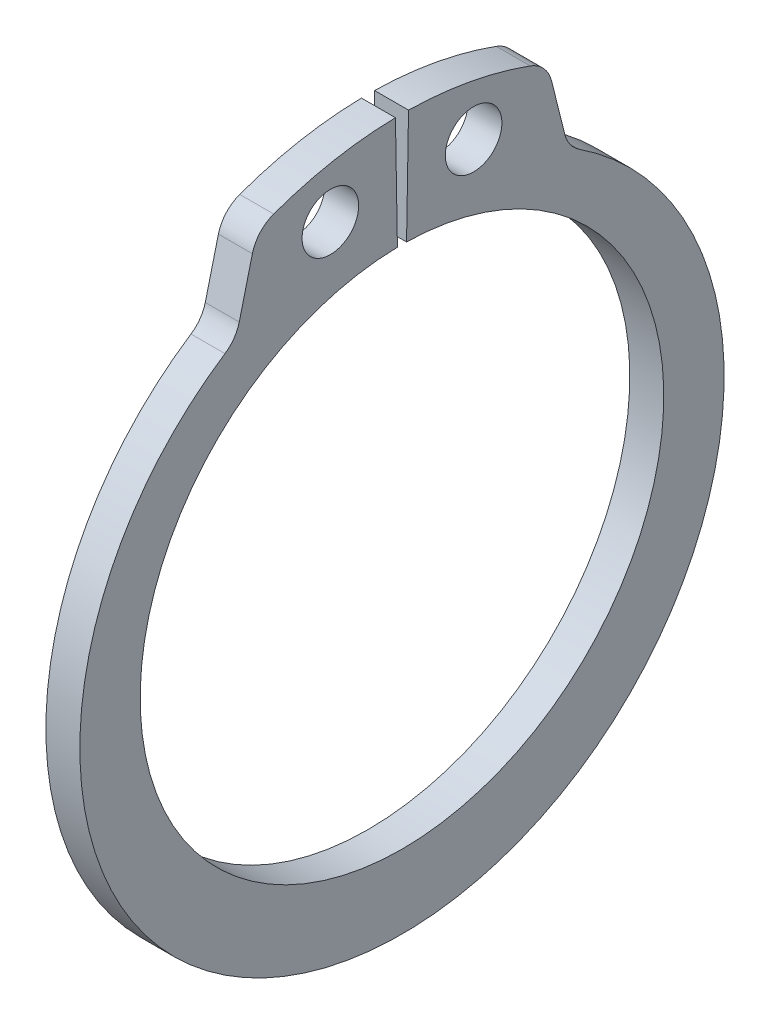
SolidWorks part; units mm, degrees
material "AISI 1045 Steel, cold drawn"
ref_plane "Front" through (0, 0, 0) normal (0, 0, 1) x (1, 0, 0)
ref_plane "Top" through (0, 0, 0) normal (0, 1, 0) x (1, 0, 0)
ref_plane "Right" through (0, 0, 0) normal (1, 0, 0) x (0, 0, -1)
sketch "Sketch1" plane through (0, 0, 0) normal (1, 0, 0) x (0, 0, -1)
  line L0 (0, 0) -> (0, 9.25) construction
  line L1 (-0.1614, 9.2486) -> (-0.2312, 13.248)
  line L2 (-0.2312, 13.248) -> (-4.8989, 13.1665) construction
  line L3 (-4.8989, 13.1665) -> (-5.8665, 9.2853) construction
  line L4 (0.2312, 13.248) -> (0.1614, 9.2486)
  line L5 (0.2312, 13.248) -> (4.8989, 13.1665) construction
  line L6 (4.8989, 13.1665) -> (5.8665, 9.2853) construction
  line L7 (-5.8665, 9.2853) -> (-4.9407, 7.82) construction
  line L8 (5.8665, 9.2853) -> (4.9407, 7.82) construction
  line L9 (0, -9.25) -> (0, -11.85) construction
  line L10 (-4.8989, 13.1665) -> (-0.1614, 9.2486) construction
  line L12 (0, 9.25) -> (0, 13.25) construction
  line L13 (5.1364, 12.2139) -> (5.8665, 9.2853)
  line L14 (-5.1364, 12.2139) -> (-5.8665, 9.2853)
  circle A0 centre (0, 0) radius 9.25 construction
  arc A1 (-0.1614, 9.2486) -> (0.1614, 9.2486) centre (0, 0) ccw
  circle A2 centre (0, -0.4681) radius 11.3819 construction
  circle A4 centre (-2.5301, 11.2075) radius 1
  circle A5 centre (2.5301, 11.2075) radius 1
  arc A6 (-5.8665, 9.2853) -> (5.8665, 9.2853) centre (0, -0.4681) ccw
  arc A7 (0.2312, 13.248) -> (5.1364, 12.2139) centre (0, 0) cw
  arc A8 (-0.2312, 13.248) -> (-5.1364, 12.2139) centre (0, 0) ccw
  dimension "A" = 18.5
  dimension "Hole" = 2
  dimension "Smin" = 1.7333
  dimension "D1" = 75
  dimension "Angle" = 1
  dimension "H" = 4
extrude "Extrude1" add sketch "Sketch1" along normal mid plane 1.2
fillet "Fillet1" radius 1.2 4 edges at (0, 9.2853, 5.8665) (0, 12.2139, 5.1364) (0, 12.2139, -5.1364) (0, 9.2853, -5.8665)
sketch "Sketch2" plane through (0, 0, 0) normal (0, 0, 1) x (1, 0, 0)
  line L0 (-3.25, 0) -> (9.75, 0)
  line L1 (9.75, 0) -> (9.75, -10)
  line L2 (-3.25, 0) -> (-3.25, -9.5)
  line L3 (9.75, -10) -> (0.65, -10)
  line L4 (0.65, -10) -> (0.65, -9.5)
  line L5 (0.65, -9.5) -> (-0.65, -9.5)
  line L6 (-0.65, -9.5) -> (-0.65, -10)
  line L7 (-0.65, -10) -> (-3.25, -10) construction
  line L8 (-3.25, -10) -> (-3.25, 0) construction
  line L9 (0, -9.5) -> (0, 0) construction
  line L10 (9.75, 0) -> (14.0551, 0) construction
  line L11 (-3.25, -9.5) -> (-2.75, -10)
  line L12 (-2.75, -10) -> (-0.65, -10)
  dimension "D2" = 13
  dimension "D3" = 3.25
  dimension "D1" = 45
revolve "Revolve1" [suppressed] add sketch "Sketch2" angle 360 about L10
equation "\"D2@Sketch2\" = \"W@Sketch2\"*10"
equation "\"D3@Sketch2\" = \"D2@Sketch2\"/4"
equation "\"Smin@Sketch1\" = \"Smax@Sketch1\"/1.5"
equation "\"D1@Fillet1\" = \"D1@Extrude1\""
